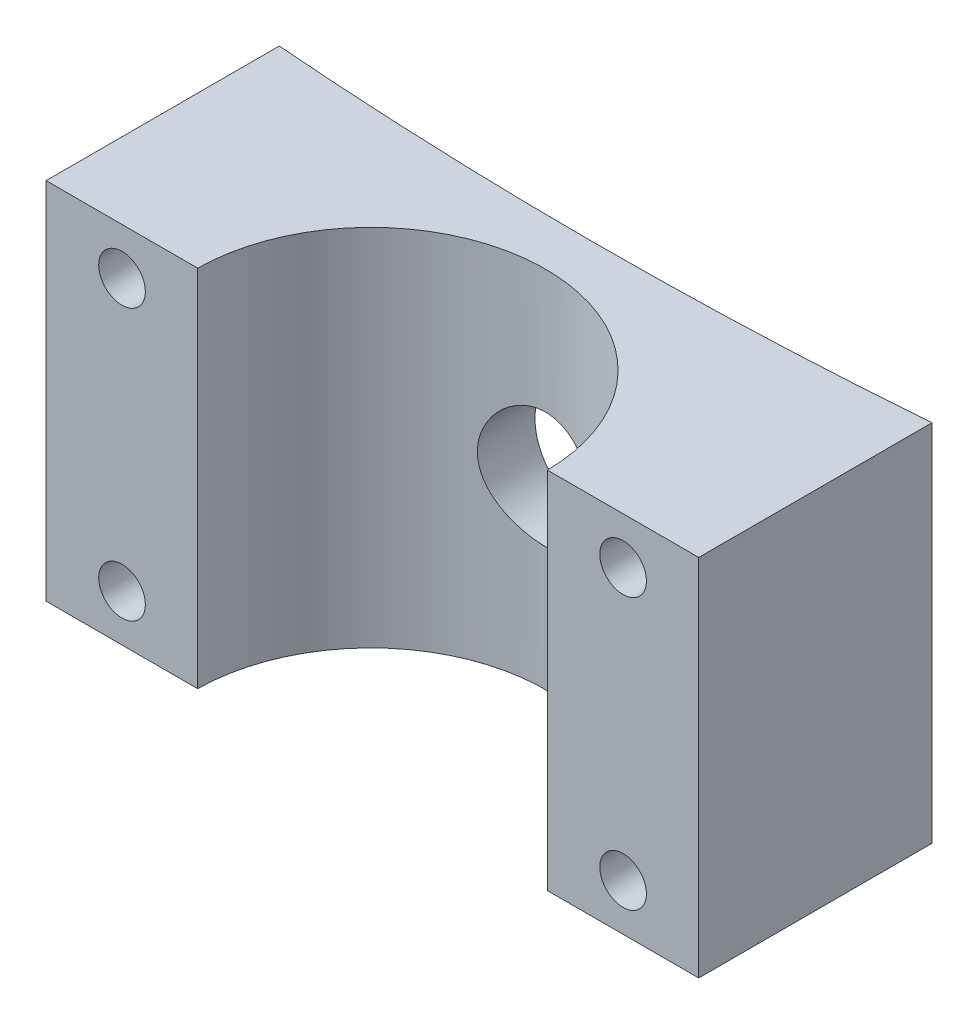
SolidWorks part; units mm, degrees
ref_plane "Front Plane" through (0, 0, 0) normal (0, 0, 1) x (1, 0, 0)
ref_plane "Top Plane" through (0, 0, 0) normal (0, 1, 0) x (1, 0, 0)
ref_plane "Right Plane" through (0, 0, 0) normal (1, 0, 0) x (0, 0, -1)
sketch "Sketch1" plane through (0, 0, 0) normal (0, 1, 0) x (1, 0, 0)
  line L0 (-630, 0) -> (630, 0) construction
  line L1 (-210.8013, -133) -> (245.5549, -133) construction
  line L2 (0, 0) -> (0, -133) construction
  line L3 (-602.5798, 17.4465) -> (-589.9243, 25.4988)
  line L4 (-616.835, -11.5296) -> (-605.5506, -21.4121)
  line L5 (616.835, -11.5296) -> (605.5506, -21.4121)
  line L6 (-140, -157.4735) -> (-140, -257.4735)
  line L7 (602.5798, 17.4465) -> (589.9243, 25.4988)
  line L8 (-140, -257.4735) -> (-74.9961, -257.4735)
  line L9 (139.8912, -257.4735) -> (139.8912, -157.4821)
  line L10 (74.9961, -257.4735) -> (139.8912, -257.4735)
  arc A0 (-616.835, -11.5296) -> (-630, -17.5) centre (-630, 0) ccw
  arc A1 (630, -17.5) -> (616.835, -11.5296) centre (630, 0) ccw
  arc A2 (-630, -17.5) -> (630, -17.5) centre (0, 1642.9318) ccw
  arc A3 (-630.0011, -32.5) -> (630.0011, -32.5) centre (0, 1627.9379) ccw
  arc A4 (-605.5506, -21.4121) -> (-630.0011, -32.5) centre (-630, 0) ccw
  arc A5 (630.0011, -32.5) -> (605.5506, -21.4121) centre (630, 0) ccw
  arc A6 (-630.0217, -47.5) -> (630.0217, -47.5) centre (0, 1613.05) ccw
  arc A7 (630.0217, -47.5) -> (589.9243, 25.4988) centre (630, 0) ccw
  arc A8 (-589.9243, 25.4988) -> (-630.0217, -47.5) centre (-630, 0) ccw
  arc A9 (139.8912, -157.4821) -> (-140, -157.4735) centre (0, 1613.05) cw
  arc A10 (74.9961, -257.4735) -> (-74.9961, -257.4735) centre (0, -258.2359) ccw
  point P5 (-630.0217, -47.5)
  point P6 (0, -163)
  point P10 (0, -133)
  point P13 (-630.0011, -32.5)
  point P14 (0, -148)
  point P15 (630.0011, -32.5)
  point P20 (630.0217, -47.5)
  dimension "D4" = 35
  dimension "D5" = 35
  dimension "D9" = 15
  dimension "D12" = 140
  dimension "D15" = 150
  dimension "D1" = 133
  dimension "D2" = 630
  dimension "D3" = 630
  dimension "D6" = 15
  dimension "D7" = 15
  dimension "D8" = 15
  dimension "D10" = 15
  dimension "D11" = 15
  dimension "D13" = 140
  dimension "D14" = 100
  dimension "D16" = 0
extrude "Boss-Extrude1" add sketch "Sketch1" along normal blind 156.2 contours A10 L10 L9 A6 L6 L8
sketch "Sketch5" plane through (0, 0, 257.4735) normal (0, 0, 1) x (1, 0, 0)
  line L0 (107.4437, 163.5921) -> (107.4437, -27.4635) construction
  line L1 (74.9961, 156.2) -> (139.8912, 156.2) construction
  line L2 (74.9961, 0) -> (139.8912, 0) construction
  line L3 (0, -85.91) -> (0, 85.91) construction
  circle A0 centre (107.4437, 136.2) radius 10
  circle A1 centre (107.4437, 20) radius 10
  circle A2 centre (-107.4437, 20) radius 10
  circle A3 centre (-107.4437, 136.2) radius 10
  dimension "D1" = 20
  dimension "D2" = 20
  dimension "D3" = 20
  dimension "D4" = 20
extrude "Cut-Extrude1" cut sketch "Sketch5" against normal through all
sketch "Sketch6" plane through (0, 0, 257.4735) normal (0, 0, 1) x (1, 0, 0)
  circle A0 centre (0, 78.1) radius 25
  dimension "D1" = 50
extrude "Cut-Extrude2" cut sketch "Sketch6" against normal through all
